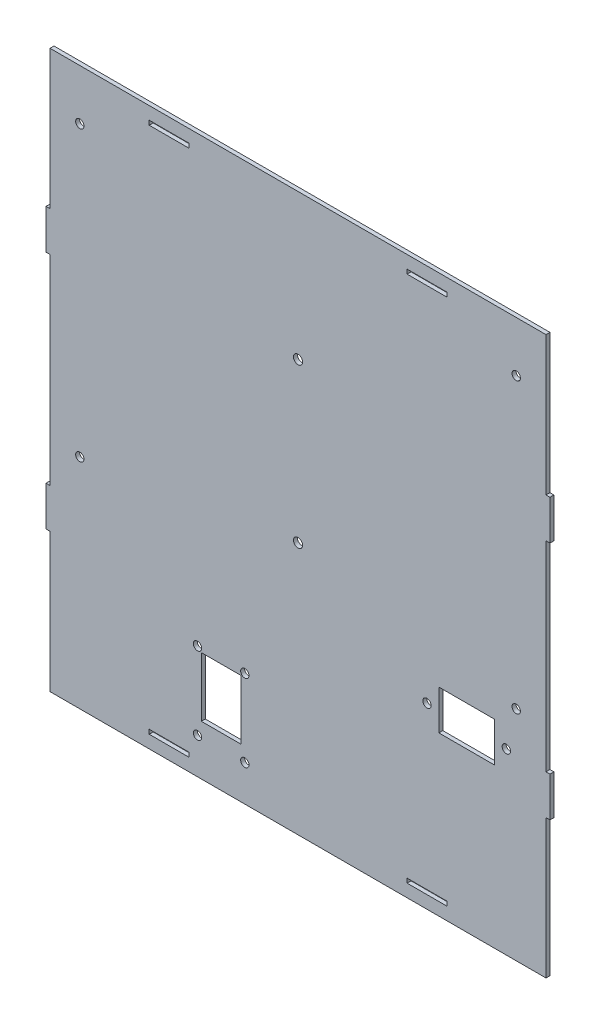
SolidWorks part; units mm, degrees
ref_plane "Front Plane" through (0, 0, 0) normal (0, 0, 1) x (1, 0, 0)
ref_plane "Top Plane" through (0, 0, 0) normal (0, 1, 0) x (1, 0, 0)
ref_plane "Right Plane" through (0, 0, 0) normal (1, 0, 0) x (0, 0, -1)
sketch "Sketch1" plane through (0, 0, 0) normal (0, 0, 1) x (1, 0, 0)
  line L1 (0, 275.4333) -> (250, 275.4333)
  line L2 (0, 275.4333) -> (0, -5.4333)
  line L3 (0, -5.4333) -> (250, -5.4333)
  line L4 (250, 275.4333) -> (250, -5.4333)
  line L5 (250, 2) -> (250, 0) construction
  line L6 (70, 267.9333) -> (50, 267.9333) construction
  line L10 (60, 0.9667) -> (60, 3.1667) construction
  line L11 (180, 2.0667) -> (200, 2.0667) construction
  line L12 (190, 0.9667) -> (190, 3.1667) construction
  line L13 (70, 2.0667) -> (50, 2.0667) construction
  line L16 (180, 0.9667) -> (200, 0.9667)
  line L17 (180, 0.9667) -> (180, 3.1667)
  line L18 (50, 0.9667) -> (50, 3.1667)
  line L19 (70, 3.1667) -> (50, 3.1667)
  line L22 (0, 2) -> (0, 0) construction
  line L23 (190, 269.0333) -> (190, 266.8333) construction
  line L24 (180, 267.9333) -> (200, 267.9333) construction
  line L25 (200, 269.0333) -> (200, 266.8333)
  line L26 (180, 266.8333) -> (200, 266.8333)
  line L27 (70, 269.0333) -> (50, 269.0333)
  line L28 (70, 269.0333) -> (70, 266.8333)
  line L29 (70, 266.8333) -> (50, 266.8333)
  line L30 (50, 269.0333) -> (50, 266.8333)
  line L31 (60, 269.0333) -> (60, 266.8333) construction
  line L32 (125, 275.4333) -> (125, -5.4333) construction
  line L33 (250, 135) -> (0, 135) construction
  line L34 (180, 269.0333) -> (180, 266.8333)
  line L35 (180, 269.0333) -> (200, 269.0333)
  line L36 (70, 0.9667) -> (70, 3.1667)
  line L37 (70, 0.9667) -> (50, 0.9667)
  line L38 (180, 3.1667) -> (200, 3.1667)
  line L39 (200, 0.9667) -> (200, 3.1667)
  circle A0 centre (125, 122.1) radius 2.3 construction
  circle A1 centre (125, 202.1) radius 2.3 construction
  circle A2 centre (125, 122.1) radius 2.3
  circle A3 centre (125, 202.1) radius 2.3
  point P26 (200, 2.0667)
  point P27 (180, 2.0667)
  point P28 (190, 0.9667)
  point P29 (190, 3.1667)
  point P30 (190, 2.0667)
  point P31 (60, 2.0667)
  point P46 (50, 267.9333)
  point P47 (70, 267.9333)
  point P48 (60, 269.0333)
  point P49 (60, 266.8333)
  point P54 (60, 267.9333)
  point P55 (125, -5.4333)
  point P56 (0, 135)
  point P57 (250, 135)
  point P64 (125, 275.4333)
  point P65 (190, 267.9333)
  point P66 (190, 266.8333)
  point P67 (190, 269.0333)
  point P68 (180, 267.9333)
  point P69 (200, 267.9333)
  point P70 (60, 3.1667)
  point P71 (60, 0.9667)
  point P72 (70, 2.0667)
  point P73 (50, 2.0667)
  dimension "D9" = 2.2
  dimension "D10" = 20
  dimension "D11" = 7.5
  dimension "D12" = 60
extrude "Boss-Extrude1" add sketch "Sketch1" along normal blind 2
sketch "Sketch2" plane through (0, 0, 2) normal (0, 0, 1) x (1, 0, 0)
  line L0 (0, 275.4333) -> (0, -5.4333) construction
  line L1 (0, 205.4333) -> (-2, 205.4333)
  line L2 (0, 205.4333) -> (0, 185.4333)
  line L3 (0, 185.4333) -> (-2, 185.4333)
  line L4 (-2, 205.4333) -> (-2, 185.4333)
  line L5 (250, -5.4333) -> (250, 275.4333) construction
  line L6 (0, 84.5667) -> (-2, 84.5667)
  line L7 (0, 84.5667) -> (0, 64.5667)
  line L8 (0, 64.5667) -> (-2, 64.5667)
  line L9 (-2, 84.5667) -> (-2, 64.5667)
  line L10 (250, 205.4333) -> (252, 205.4333)
  line L11 (250, 205.4333) -> (250, 185.4333)
  line L12 (250, 185.4333) -> (252, 185.4333)
  line L13 (252, 205.4333) -> (252, 185.4333)
  line L14 (250, 275.4333) -> (0, 275.4333) construction
  line L15 (250, 84.5667) -> (252, 84.5667)
  line L16 (250, 84.5667) -> (250, 64.5667)
  line L17 (250, 64.5667) -> (252, 64.5667)
  line L18 (252, 84.5667) -> (252, 64.5667)
  line L19 (0, -5.4333) -> (250, -5.4333) construction
  dimension "D1" = 2
  dimension "D2" = 20
  dimension "D3" = 70
  dimension "D4" = 70
extrude "Boss-Extrude2" add sketch "Sketch2" against normal up to surface (2 mm away) up to face at (190, 267.9333, 0)
sketch "Sketch3" plane through (0, 0, 2) normal (0, 0, 1) x (1, 0, 0)
  line L0 (210, 94.5667) -> (210, 74.5667) construction
  line L1 (196, 94.5667) -> (224, 94.5667)
  line L2 (196, 94.5667) -> (196, 74.5667)
  line L3 (196, 74.5667) -> (224, 74.5667)
  line L4 (224, 94.5667) -> (224, 74.5667)
  line L5 (250, 2) -> (250, 77) construction
  line L6 (0, -5.4333) -> (250, -5.4333) construction
  circle A0 centre (190, 84.5667) radius 2.1
  circle A1 centre (230, 84.5667) radius 2.1
  dimension "D3" = 4.2
  dimension "D4" = 4.2
  dimension "D5" = 40
  dimension "D6" = 20
  dimension "D7" = 10
  dimension "D1" = 28
  dimension "D2" = 20
  dimension "D8" = 40
  dimension "D9" = 80
extrude "Cut-Extrude1" cut sketch "Sketch3" against normal blind 5
sketch "Sketch4" plane through (0, 0, 2) normal (0, 0, 1) x (1, 0, 0)
  line L0 (0, 64.5667) -> (0, -5.4333) construction
  line L1 (76.25, 49.7667) -> (96.25, 49.7667)
  line L2 (76.25, 49.7667) -> (76.25, 19.7667)
  line L3 (76.25, 19.7667) -> (96.25, 19.7667)
  line L4 (96.25, 49.7667) -> (96.25, 19.7667)
  line L5 (0, -5.4333) -> (250, -5.4333) construction
  dimension "D1" = 20
  dimension "D2" = 30
  dimension "D3" = 76.25
  dimension "D4" = 25.2
extrude "Cut-Extrude2" cut sketch "Sketch4" against normal blind 5
sketch "Sketch5" plane through (0, 0, 2) normal (0, 0, 1) x (1, 0, 0)
  circle A0 centre (98.1863, 12.72) radius 2.1 construction
  circle A1 centre (74.3137, 12.72) radius 2.1 construction
  circle A2 centre (74.3137, 51.68) radius 2.1 construction
  circle A3 centre (98.1863, 51.68) radius 2.1 construction
  circle A4 centre (98.1863, 12.72) radius 2.1
  circle A5 centre (74.3137, 12.72) radius 2.1
  circle A6 centre (74.3137, 51.68) radius 2.1
  circle A7 centre (98.1863, 51.68) radius 2.1
extrude "Cut-Extrude3" cut sketch "Sketch5" against normal through all
sketch "Sketch6" plane through (0, 0, 2) normal (0, 0, 1) x (1, 0, 0)
  line L0 (200, 265) -> (250, 265) construction
  line L2 (250, -5.4333) -> (250, 275.4333) construction
  line L3 (0, 265) -> (50, 265) construction
  line L4 (0, 255) -> (0, 265) construction
  circle A0 centre (235, 250) radius 2.1
  circle A1 centre (15, 250) radius 2.1
  dimension "D1" = 15
  dimension "D3" = 4.2
  dimension "D4" = 4.2
  dimension "D5" = 15
  dimension "D6" = 15
  dimension "D2" = 15
extrude "Cut-Extrude4" cut sketch "Sketch6" against normal blind 5
sketch "Sketch7" plane through (0, 0, 2) normal (0, 0, 1) x (1, 0, 0)
  line L0 (0, -5.4333) -> (0, 275.4333) construction
  line L1 (0, -5.4333) -> (250, -5.4333) construction
  line L2 (250, 84.5667) -> (250, 185.4333) construction
  circle A0 centre (15, 104.5667) radius 2.1
  circle A1 centre (235, 104.5667) radius 2.1
  dimension "D1" = 4.2
  dimension "D4" = 4.2
  dimension "D5" = 15
  dimension "D6" = 110
  dimension "D2" = 15
  dimension "D3" = 110
extrude "Cut-Extrude5" cut sketch "Sketch7" against normal blind 5
